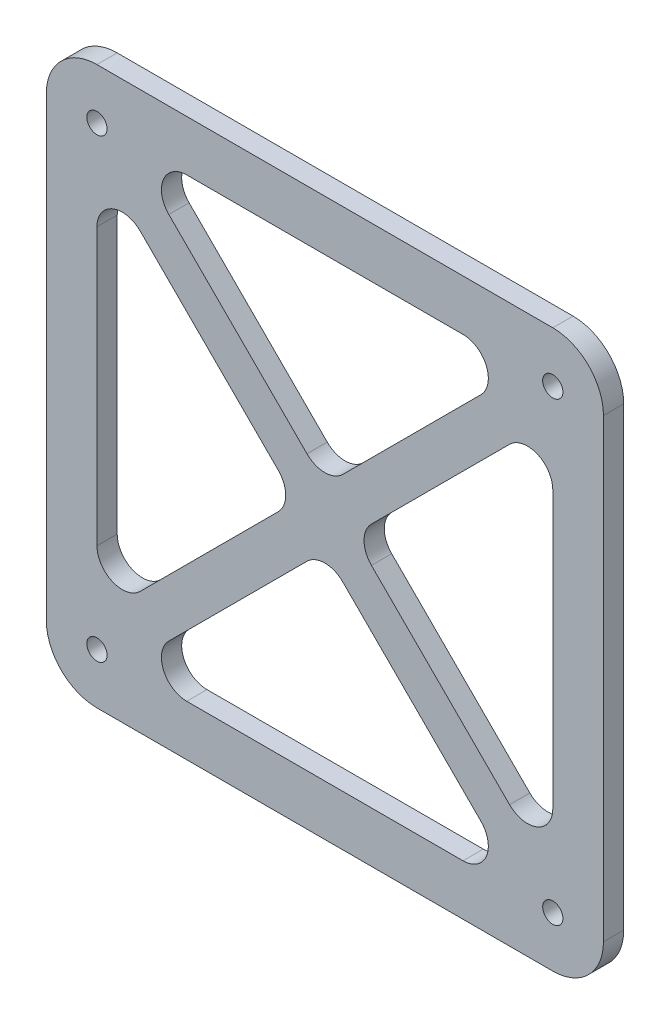
SolidWorks part; units mm, degrees
material "Hexcel AS4C (3000 Filaments)"
ref_plane "Front Plane" through (0, 0, 0) normal (0, 0, 1) x (1, 0, 0)
ref_plane "Top Plane" through (0, 0, 0) normal (0, 1, 0) x (1, 0, 0)
ref_plane "Right Plane" through (0, 0, 0) normal (1, 0, 0) x (0, 0, -1)
sketch "Sketch1" plane through (0, 0, 0) normal (0, 0, 1) x (1, 0, 0)
  line L0 (0, 0) -> (0, 42.3983) construction
  line L1 (22.5, 27.5) -> (-22.5, 27.5)
  line L2 (27.5, 22.5) -> (27.5, -22.5)
  line L3 (22.5, -27.5) -> (-22.5, -27.5)
  line L4 (-27.5, 22.5) -> (-27.5, -22.5)
  line L5 (27.5, 27.5) -> (-27.5, -27.5) construction
  line L6 (27.5, -27.5) -> (-27.5, 27.5) construction
  line L7 (-13.636, 22.5) -> (13.636, 22.5)
  line L8 (15.4038, 18.2322) -> (1.7678, 4.5962)
  line L9 (-1.7678, 4.5962) -> (-15.4038, 18.2322)
  line L10 (-18.2322, 15.4038) -> (-4.5962, 1.7678)
  line L11 (-4.5962, -1.7678) -> (-18.2322, -15.4038)
  line L12 (-22.5, -13.636) -> (-22.5, 13.636)
  line L13 (-15.4038, -18.2322) -> (-1.7678, -4.5962)
  line L14 (1.7678, -4.5962) -> (15.4038, -18.2322)
  line L15 (13.636, -22.5) -> (-13.636, -22.5)
  line L16 (18.2322, -15.4038) -> (4.5962, -1.7678)
  line L17 (4.5962, 1.7678) -> (18.2322, 15.4038)
  line L18 (22.5, 13.636) -> (22.5, -13.636)
  arc A0 (-22.5, 27.5) -> (-27.5, 22.5) centre (-22.5, 22.5) ccw
  arc A1 (-27.5, -22.5) -> (-22.5, -27.5) centre (-22.5, -22.5) ccw
  arc A2 (22.5, -27.5) -> (27.5, -22.5) centre (22.5, -22.5) ccw
  arc A3 (27.5, 22.5) -> (22.5, 27.5) centre (22.5, 22.5) ccw
  circle A4 centre (-22.5, 22.5) radius 1
  circle A5 centre (22.5, 22.5) radius 1
  circle A6 centre (22.5, -22.5) radius 1
  circle A7 centre (-22.5, -22.5) radius 1
  arc A8 (13.636, 22.5) -> (15.4038, 18.2322) centre (13.636, 20) cw
  arc A12 (1.7678, 4.5962) -> (-1.7678, 4.5962) centre (0, 6.364) cw
  arc A13 (-15.4038, 18.2322) -> (-13.636, 22.5) centre (-13.636, 20) cw
  arc A14 (-18.2322, -15.4038) -> (-22.5, -13.636) centre (-20, -13.636) cw
  arc A15 (-22.5, 13.636) -> (-18.2322, 15.4038) centre (-20, 13.636) cw
  arc A16 (-4.5962, 1.7678) -> (-4.5962, -1.7678) centre (-6.364, 0) cw
  arc A17 (15.4038, -18.2322) -> (13.636, -22.5) centre (13.636, -20) cw
  arc A18 (-13.636, -22.5) -> (-15.4038, -18.2322) centre (-13.636, -20) cw
  arc A19 (-1.7678, -4.5962) -> (1.7678, -4.5962) centre (0, -6.364) cw
  arc A20 (18.2322, 15.4038) -> (22.5, 13.636) centre (20, 13.636) cw
  arc A21 (22.5, -13.636) -> (18.2322, -15.4038) centre (20, -13.636) cw
  arc A22 (4.5962, -1.7678) -> (4.5962, 1.7678) centre (6.364, 0) cw
  point P0 (0, 0)
  point P22 (0, 0)
  point P25 (0, 0)
  point P28 (0, 0)
  point P31 (0, 0)
  point P41 (0, 0)
  point P45 (0, 2.8284)
  point P78 (0, 0)
  dimension "D3" = 5
  dimension "D4" = 4
  dimension "D5" = 5
  dimension "D6" = 4
  dimension "D8" = 2.5
  dimension "D1" = 55
  dimension "D2" = 55
  dimension "D7" = 2
extrude "Boss-Extrude1" add sketch "Sketch1" along normal blind 2
